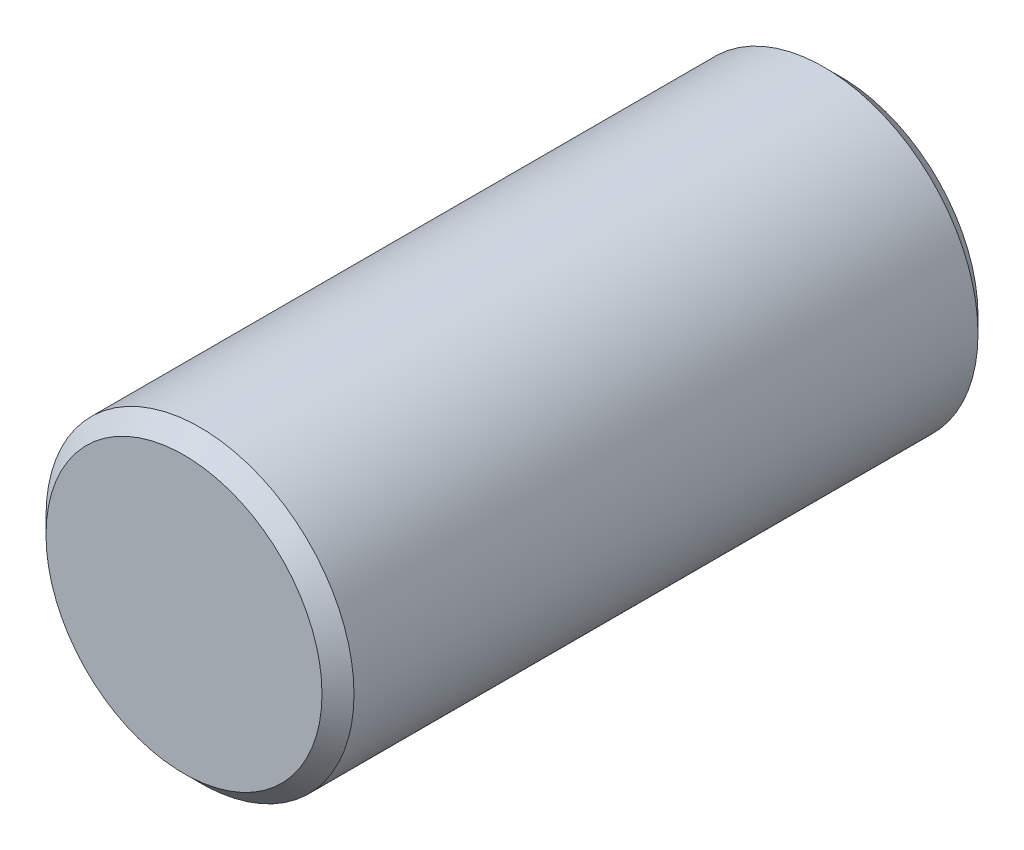
SolidWorks part; units mm, degrees
ref_plane "Front Plane" through (0, 0, 0) normal (0, 0, 1) x (1, 0, 0)
ref_plane "Top Plane" through (0, 0, 0) normal (0, 1, 0) x (1, 0, 0)
ref_plane "Right Plane" through (0, 0, 0) normal (1, 0, 0) x (0, 0, -1)
sketch "Sketch1" plane through (0, 0, 0) normal (0, 0, 1) x (1, 0, 0)
  circle A0 centre (0, 0) radius 19.25
  dimension "D1" = 38.5
extrude "Boss-Extrude1" add sketch "Sketch1" along normal mid plane 82
chamfer "Chamfer1" distance 2 angle 45 2 edges at (19.25, 0, 41) (19.25, 0, -41)
